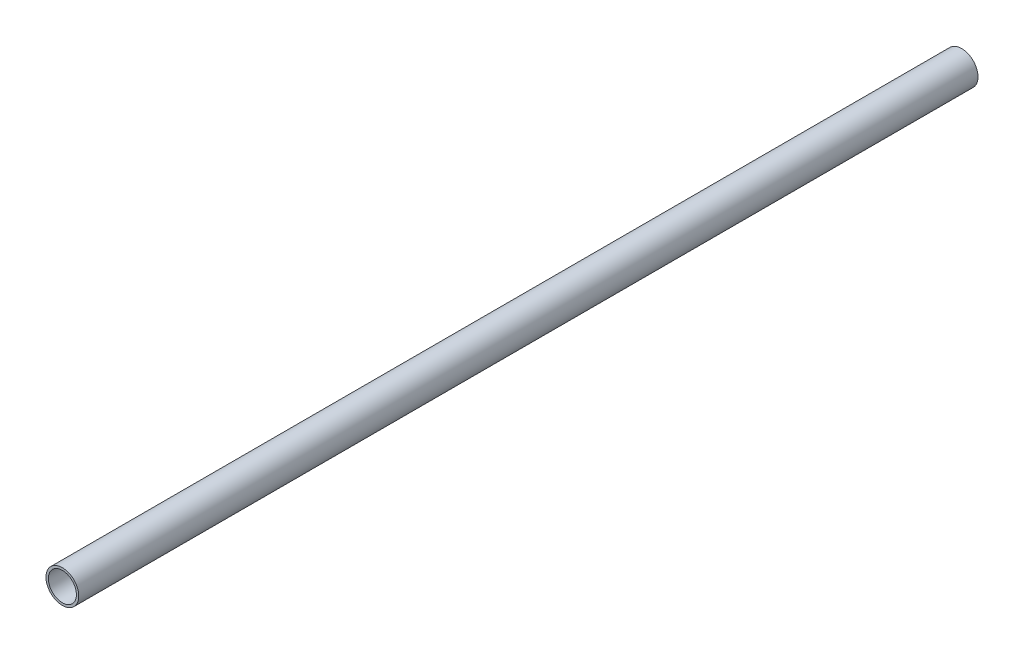
SolidWorks part; units mm, degrees
material "Thornel VCB-20 Carbon Cloth"
ref_plane "Front Plane" through (0, 0, 0) normal (0, 0, 1) x (1, 0, 0)
ref_plane "Top Plane" through (0, 0, 0) normal (0, 1, 0) x (1, 0, 0)
ref_plane "Right Plane" through (0, 0, 0) normal (1, 0, 0) x (0, 0, -1)
sketch "Sketch1" plane through (0, 0, 0) normal (0, 0, 1) x (1, 0, 0)
  circle A0 centre (0, 0) radius 9.525
  circle A1 centre (0, 0) radius 11.1125
  dimension "D1" = 19.05
  dimension "D2" = 22.225
extrude "Boss-Extrude1" add sketch "Sketch1" along normal mid plane 609.6
